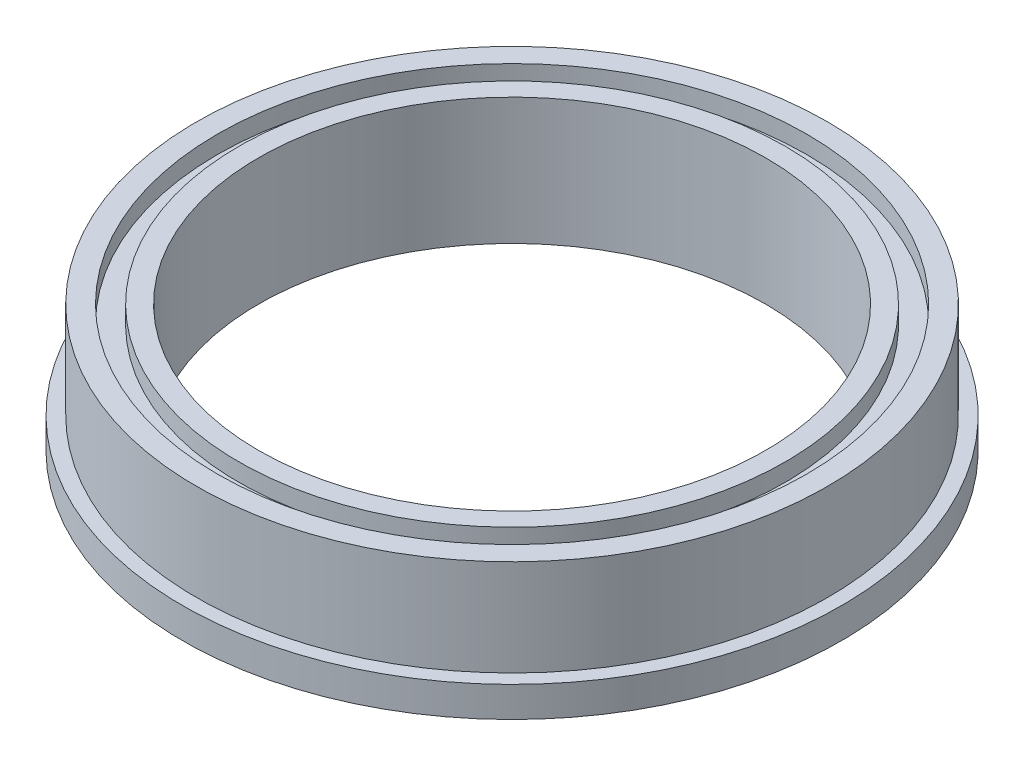
SolidWorks part; units mm, degrees
ref_plane "Front Plane" through (0, 0, 0) normal (0, 0, 1) x (1, 0, 0)
ref_plane "Top Plane" through (0, 0, 0) normal (0, 1, 0) x (1, 0, 0)
ref_plane "Right Plane" through (0, 0, 0) normal (1, 0, 0) x (0, 0, -1)
sketch "Sketch1" plane through (0, 0, 0) normal (0, 0, 1) x (1, 0, 0)
  line L0 (16.51, 0) -> (16.51, 1.524)
  line L1 (16.51, 1.524) -> (15.8115, 1.524)
  line L2 (15.8115, 1.524) -> (15.8115, 6.35)
  line L3 (15.8115, 6.35) -> (14.7574, 6.35)
  line L4 (14.7574, 6.35) -> (14.7574, 5.461)
  line L5 (14.7574, 5.461) -> (13.6906, 5.461)
  line L6 (13.6906, 5.461) -> (13.6906, 6.35)
  line L7 (13.6906, 6.35) -> (12.7, 6.35)
  line L8 (12.7, 6.35) -> (12.7, 0)
  line L9 (12.7, 0) -> (13.6906, 0)
  line L10 (13.6906, 0) -> (13.6906, 0.889)
  line L11 (13.6906, 0.889) -> (14.7574, 0.889)
  line L12 (14.7574, 0.889) -> (14.7574, 0)
  line L13 (14.7574, 0) -> (16.51, 0)
  line L14 (0, 6.35) -> (0, 0) construction
  dimension "D1" = 12.7
  dimension "D2" = 13.6906
  dimension "D3" = 14.7574
  dimension "D4" = 15.8115
  dimension "D5" = 16.51
  dimension "D6" = 0.889
  dimension "D7" = 1.524
  dimension "D8" = 5.461
revolve "Revolve1" add sketch "Sketch1" angle 360 about L14
